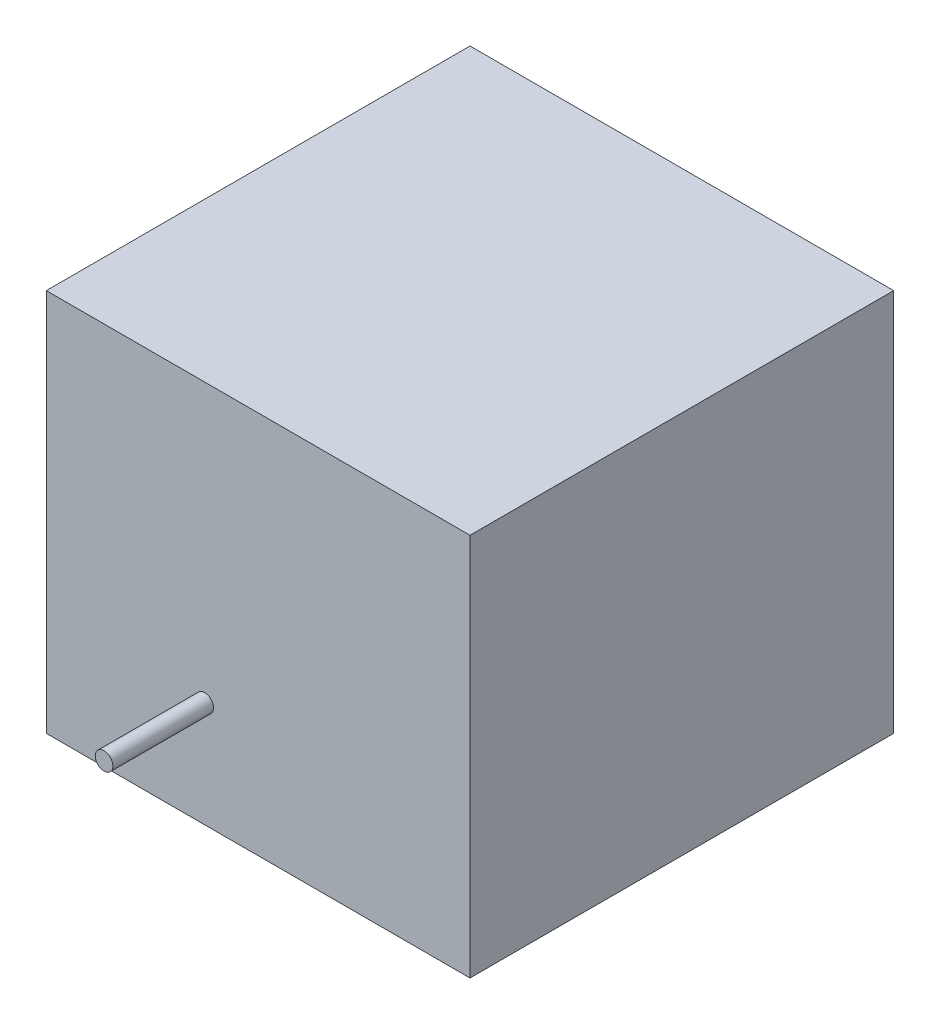
SolidWorks part; units mm, degrees
ref_plane "Front Plane" through (0, 0, 0) normal (0, 0, 1) x (1, 0, 0)
ref_plane "Top Plane" through (0, 0, 0) normal (0, 1, 0) x (1, 0, 0)
ref_plane "Right Plane" through (0, 0, 0) normal (1, 0, 0) x (0, 0, -1)
sketch "Sketch2" plane through (0, 0, 0) normal (0, 1, 0) x (1, 0, 0)
  line L1 (0, 0) -> (42.1, 0)
  line L2 (0, 0) -> (0, 42.1)
  line L3 (0, 42.1) -> (42.1, 42.1)
  line L4 (42.1, 0) -> (42.1, 42.1)
  dimension "D1" = 42.1
  dimension "D2" = 42.1
extrude "Boss-Extrude1" add sketch "Sketch2" along normal blind 38.1
sketch "Sketch4" plane through (0, 0, 0) normal (0, 0, 1) x (1, 0, 0)
  line L2 (0, 0) -> (42.1, 0) construction
  line L8 (42.1, 38.1) -> (42.1, 0) construction
  circle A1 centre (15.74, 10.5) radius 0.875
  dimension "D1" = 10.5
  dimension "D3" = 1.75
  dimension "D2" = 26.36
extrude "Boss-Extrude2" add sketch "Sketch4" along normal blind 10
sketch "Sketch5" plane through (0, 0, -42.1) normal (0, 0, -1) x (-1, 0, 0)
  circle A1 centre (-15.74, 10.5) radius 0.875
  circle A2 centre (-15.74, 10.5) radius 0.875
  dimension "D1" = 0
extrude "Boss-Extrude3" add sketch "Sketch5" along normal blind 15
